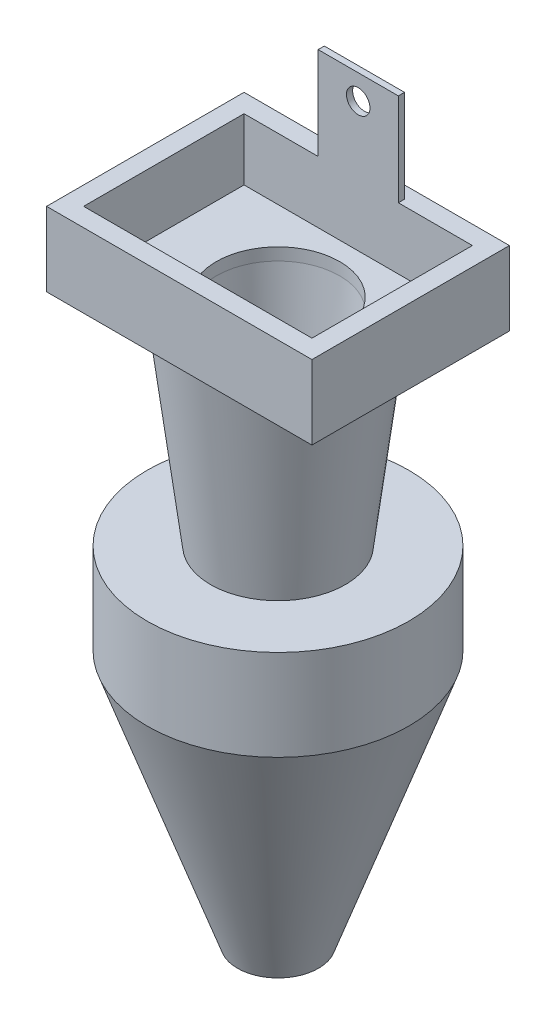
SolidWorks part; units mm, degrees
ref_plane "Front Plane" through (0, 0, 0) normal (0, 0, 1) x (1, 0, 0)
ref_plane "Top Plane" through (0, 0, 0) normal (0, 1, 0) x (1, 0, 0)
ref_plane "Right Plane" through (0, 0, 0) normal (1, 0, 0) x (0, 0, -1)
sketch "Sketch1" plane through (0, 0, 0) normal (0, 1, 0) x (1, 0, 0)
  line L1 (0, 0) -> (37, 0)
  line L2 (0, 0) -> (0, 26)
  line L3 (0, 26) -> (37, 26)
  line L4 (37, 0) -> (37, 26)
  line L5 (-3, -3) -> (40, -3)
  line L6 (-3, -3) -> (-3, 29)
  line L7 (-3, 29) -> (40, 29)
  line L8 (40, -3) -> (40, 29)
  dimension "D1" = 26
  dimension "D2" = 37
  dimension "D3" = 3
  dimension "D4" = 3
  dimension "D5" = 3
  dimension "D6" = 3
extrude "Boss-Extrude1" add sketch "Sketch1" along normal blind 10
sketch "Sketch2" plane through (0, 10, 0) normal (0, 1, 0) x (1, 0, 0)
  line L0 (37, 26) -> (0, 26) construction
  line L1 (25, 26) -> (12, 26)
  line L2 (25, 26) -> (25, 27)
  line L3 (25, 27) -> (12, 27)
  line L4 (12, 26) -> (12, 27)
  line L5 (40, -3) -> (40, 29) construction
  line L6 (-3, 29) -> (-3, -3) construction
  dimension "D1" = 1
  dimension "D2" = 15
  dimension "D3" = 15
extrude "Boss-Extrude2" add sketch "Sketch2" along normal blind 15
sketch "Sketch3" plane through (0, 0, -27) normal (0, 0, -1) x (-1, 0, 0)
  line L0 (-25, 25) -> (-12, 25) construction
  line L1 (-25, 25) -> (-25, 10) construction
  circle A0 centre (-18.5, 21) radius 1.905
  dimension "D1" = 3.81
  dimension "D2" = 4
  dimension "D3" = 6.5
extrude "Cut-Extrude1" cut sketch "Sketch3" against normal up to next
sketch "Sketch4" plane through (0, 0, 0) normal (0, -1, 0) x (1, 0, 0)
  line L1 (40, -29) -> (-3, -29)
  line L2 (40, -29) -> (40, 3)
  line L3 (40, 3) -> (-3, 3)
  line L4 (-3, -29) -> (-3, 3)
extrude "Boss-Extrude3" add sketch "Sketch4" along normal blind 2
sketch "Sketch5" plane through (0, -2, 0) normal (0, -1, 0) x (1, 0, 0)
  line L0 (-3, -29) -> (40, -29) construction
  line L2 (-3, 3) -> (-3, -29) construction
  circle A0 centre (18.5, -13) radius 10
  dimension "D1" = 16
  dimension "D2" = 21.5
extrude "Cut-Extrude2" cut sketch "Sketch5" against normal up to next
sketch "Sketch8" plane through (0, -2, 0) normal (0, -1, 0) x (1, 0, 0)
  line L0 (-3, -13) -> (40, -13) construction
  line L1 (-3, 3) -> (-3, -29) construction
  line L2 (40, -29) -> (40, 3) construction
  point P0 (18.5, -13)
ref_plane "Plane1" through (0, 0, -13) normal (0, 0, 1) x (1, 0, 0)
sketch "Sketch9" plane through (0, 0, -13) normal (0, 0, 1) x (1, 0, 0)
  line L0 (28.5, -2) -> (21.5, -90.9)
  line L1 (21.5, -90.9) -> (22.5, -90.9)
  line L2 (22.5, -90.9) -> (33.5, -2)
  line L3 (33.5, -2) -> (28.5, -2)
  line L4 (-3, -2) -> (40, -2) construction
  dimension "D1" = 1
  dimension "D2" = 3
  dimension "D3" = 88.9
  dimension "D4" = 5
ref_axis "Axis1" through (18.5, -2, -13) along (0, -1, 0)
revolve "Revolve1" add sketch "Sketch9" angle 360 about axis through (18.5, -2, -13) along (0, -1, 0)
sketch "Sketch10" plane through (0, 0, -13) normal (0, 0, 1) x (1, 0, 0)
  line L0 (12.9886, -90.9) -> (8.6332, -49.593)
  line L1 (8.6332, -49.593) -> (0.379, -49.593)
  line L2 (-2.6969, -49.593) -> (11.9356, -90.9)
  line L3 (11.9356, -90.9) -> (12.9886, -90.9)
  line L4 (-2.6969, -49.593) -> (-2.6969, -34.8699)
  line L5 (-2.6969, -34.8699) -> (7.5671, -34.8699)
  line L6 (3.5, -2) -> (14.5, -90.9) construction
  line L7 (7.5671, -34.8699) -> (8.0031, -38.393)
  line L8 (8.0031, -38.393) -> (0.379, -38.393)
  line L9 (0.379, -38.393) -> (0.379, -49.593)
  line L10 (14.5, -90.9) -> (22.5, -90.9) construction
  point P2 (6.3467, -50.7915)
  point P12 (-6.2838, -50.2433)
  point P13 (-3.6321, -48.1213)
  point P14 (5.8658, -49.4676)
  point P15 (-1.687, -47.626)
  point P16 (7.5671, -49.6708)
  point P17 (-6.2838, -47.4942)
  point P18 (-6.2838, -38.393)
  point P19 (0, 0)
  point P20 (8.0031, -49.671)
  point P23 (-2.6969, -49.593)
  point P24 (0.379, -49.593)
  dimension "D1" = 0.75
  dimension "D2" = 1.5
  dimension "D3" = 0
revolve "Revolve2" add sketch "Sketch10" angle 360 about axis through (18.5, -2, -13) along (0, -1, 0)
sketch "Sketch11" plane through (-3, 0, 0) normal (-1, 0, 0) x (0, 0, 1)
  circle A0 centre (-16.2172, -43.6109) radius 3.175
extrude "Cut-Extrude3" cut sketch "Sketch11" against normal blind 15 from offset 10
